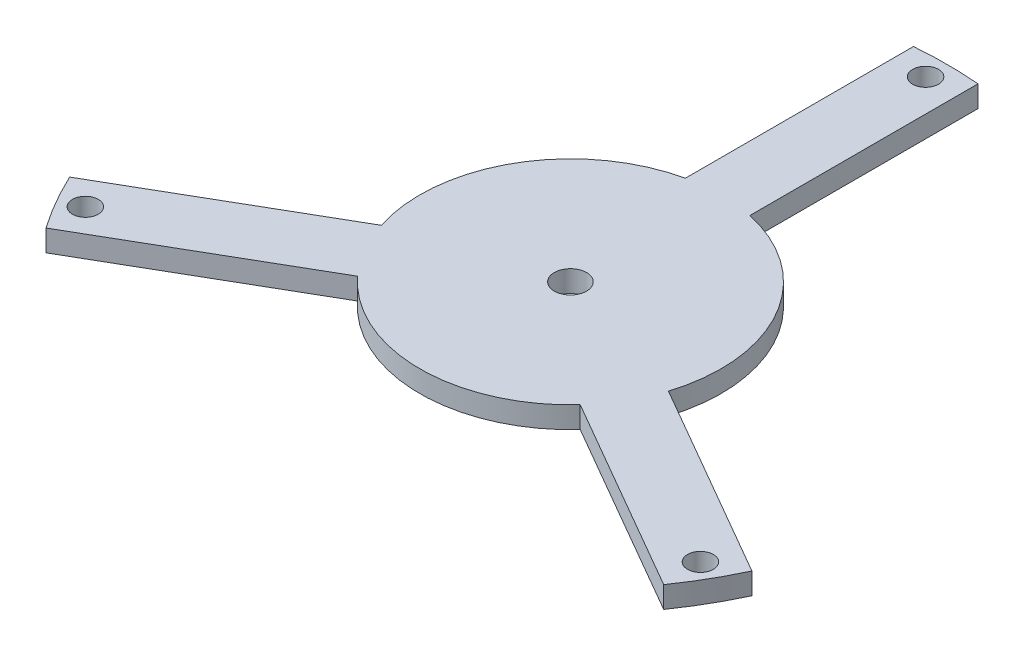
SolidWorks part; units mm, degrees
ref_plane "前视基准面" through (0, 0, 0) normal (0, 0, 1) x (1, 0, 0)
ref_plane "上视基准面" through (0, 0, 0) normal (0, 1, 0) x (1, 0, 0)
ref_plane "右视基准面" through (0, 0, 0) normal (1, 0, 0) x (0, 0, -1)
sketch "草图1" plane through (0, 0, 0) normal (0, 1, 0) x (1, 0, 0)
  line L0 (-276.4363, 0) -> (296.8125, 0) construction
  line L1 (0, 178.9705) -> (0, -181.6873) construction
  line L2 (158.4967, -74.1876) -> (66.7136, -21.1966)
  line L3 (143.4967, -100.1684) -> (51.7136, -47.1774)
  line L4 (-15, 174.356) -> (-15, 68.374)
  line L5 (-143.4967, -100.1684) -> (-51.7136, -47.1774)
  line L6 (15, 174.356) -> (15, 68.374)
  line L7 (-158.4967, -74.1876) -> (-66.7136, -21.1966)
  arc A0 (143.4967, -100.1684) -> (158.4967, -74.1876) centre (0, 0) ccw
  arc A1 (134.8025, -95.1488) -> (149.8025, -69.168) centre (0, 0) ccw construction
  arc A3 (-15, 68.374) -> (-66.7136, -21.1966) centre (0, 0) ccw
  circle A4 centre (0, 165) radius 6
  circle A5 centre (142.8942, -82.5) radius 6
  circle A6 centre (-142.8942, -82.5) radius 6
  arc A7 (-51.7136, -47.1774) -> (51.7136, -47.1774) centre (0, 0) ccw
  arc A8 (15, 164.3168) -> (-15, 164.3168) centre (0, 0) ccw construction
  arc A9 (66.7136, -21.1966) -> (15, 68.374) centre (0, 0) ccw
  arc A11 (15, 174.356) -> (-15, 174.356) centre (0, 0) ccw
  arc A12 (-149.8025, -69.168) -> (-134.8025, -95.1488) centre (0, 0) ccw construction
  arc A13 (-158.4967, -74.1876) -> (-143.4967, -100.1684) centre (0, 0) ccw
  point P19 (0, 0)
  point P30 (0, 0)
  dimension "D1" = 350
  dimension "D2" = 330
  dimension "D3" = 30
  dimension "D4" = 140
  dimension "D5" = 12
  dimension "D8" = 3
  dimension "D6" = 3
extrude "凸台-拉伸1" add sketch "草图1" along normal blind 10
sketch "草图2" plane through (0, 10, 0) normal (0, 1, 0) x (1, 0, 0)
  circle A0 centre (0, 0) radius 7.5
  dimension "D1" = 15
extrude "切除-拉伸1" cut sketch "草图2" against normal through all contours A0
